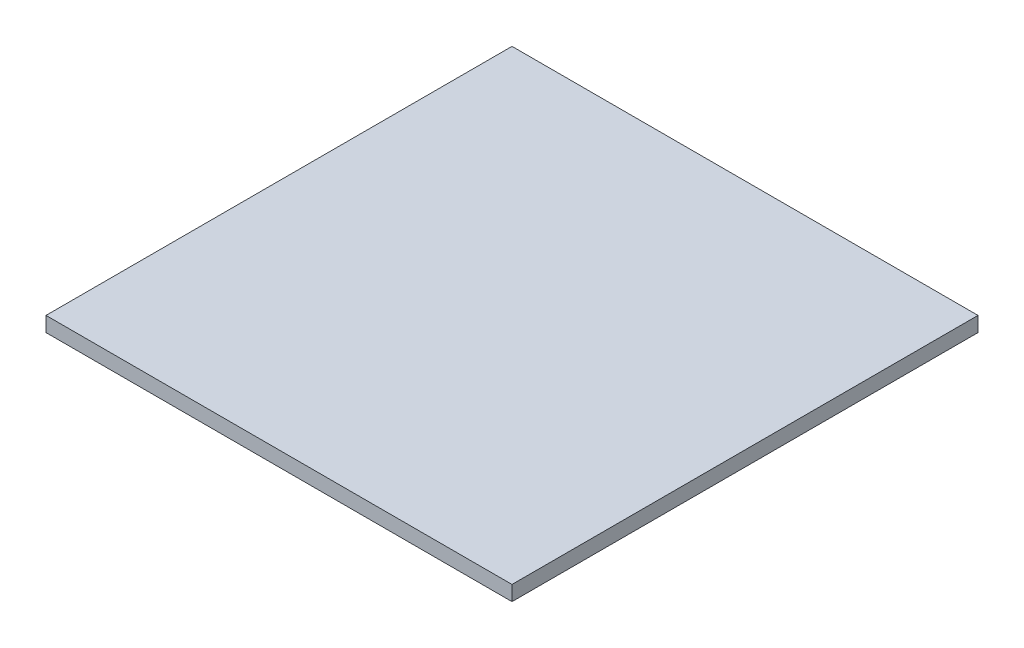
SolidWorks part; units mm, degrees
ref_plane "Front Plane" through (0, 0, 0) normal (0, 0, 1) x (1, 0, 0)
ref_plane "Top Plane" through (0, 0, 0) normal (0, 1, 0) x (1, 0, 0)
ref_plane "Right Plane" through (0, 0, 0) normal (1, 0, 0) x (0, 0, -1)
sketch "Sketch1" plane through (0, 0, 0) normal (0, 1, 0) x (1, 0, 0)
  line L0 (-33.963, 0) -> (34.2991, 0) construction
  line L1 (-25, 25) -> (25, 25)
  line L2 (-25, 25) -> (-25, -25)
  line L3 (-25, -25) -> (25, -25)
  line L4 (25, 25) -> (25, -25)
  line L5 (0, 30.5452) -> (0, -33.5102) construction
  line L6 (1.65, -6.95) -> (1.65, -2.25) construction
  line L7 (-1.65, 6.95) -> (1.65, 6.95) construction
  line L8 (-1.65, 6.95) -> (-1.65, 2.25) construction
  line L9 (-1.65, 2.25) -> (1.65, 2.25) construction
  line L10 (1.65, 6.95) -> (1.65, 2.25) construction
  line L11 (-1.65, -2.25) -> (1.65, -2.25) construction
  line L12 (-1.65, -6.95) -> (-1.65, -2.25) construction
  line L13 (-1.65, -6.95) -> (1.65, -6.95) construction
  dimension "D1" = 50
  dimension "D2" = 50
  dimension "D3" = 3.3
  dimension "D4" = 4.7
  dimension "D5" = 4.5
extrude "Boss-Extrude1" add sketch "Sketch1" along normal blind 1.6
